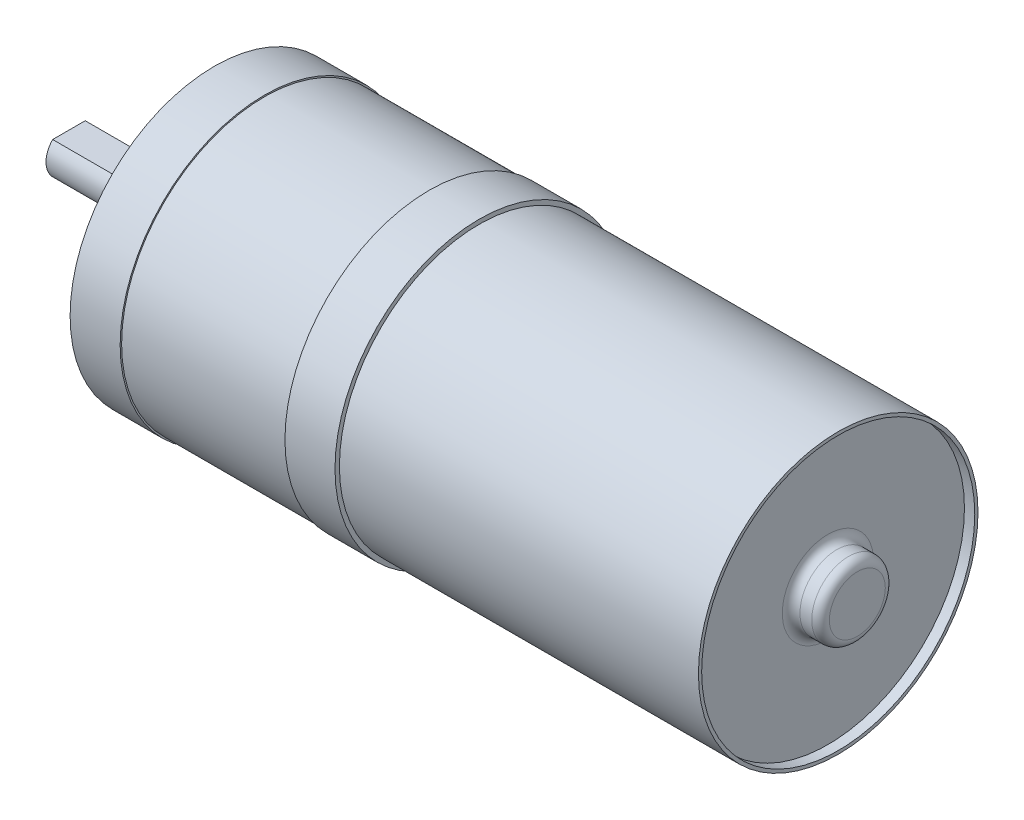
SolidWorks part; units mm, degrees
ref_plane "Front Plane" through (0, 0, 0) normal (0, 0, 1) x (1, 0, 0)
ref_plane "Top Plane" through (0, 0, 0) normal (0, 1, 0) x (1, 0, 0)
ref_plane "Right Plane" through (0, 0, 0) normal (1, 0, 0) x (0, 0, -1)
sketch "Sketch1" plane through (0, 0, 0) normal (1, 0, 0) x (0, 0, -1)
  circle A0 centre (0, 0) radius 12.065
extrude "Boss-Extrude1" add sketch "Sketch1" along normal blind 30.988
sketch "Sketch2" plane through (0, 0, 0) normal (-1, 0, 0) x (0, 0, 1)
  circle A0 centre (0, 0) radius 12.446
extrude "Boss-Extrude2" add sketch "Sketch2" along normal blind 4.318
sketch "Sketch3" plane through (-4.318, 0, 0) normal (-1, 0, 0) x (0, 0, 1)
  circle A0 centre (0, 0) radius 12.319
extrude "Boss-Extrude3" add sketch "Sketch3" along normal blind 14.224
sketch "Sketch4" plane through (-18.542, 0, 0) normal (-1, 0, 0) x (0, 0, 1)
  circle A0 centre (0, 0) radius 12.446
extrude "Boss-Extrude4" add sketch "Sketch4" along normal blind 4.318
sketch "Sketch5" plane through (-22.86, 0, 0) normal (-1, 0, 0) x (0, 0, 1)
  circle A0 centre (0, 0) radius 3.5052
extrude "Boss-Extrude5" add sketch "Sketch5" along normal blind 2.54
sketch "Sketch6" plane through (-25.4, 0, 0) normal (-1, 0, 0) x (0, 0, 1)
  circle A0 centre (0, 0) radius 1.9812
extrude "Boss-Extrude6" add sketch "Sketch6" along normal blind 10.0076
sketch "Sketch7" plane through (-35.4076, 0, 0) normal (-1, 0, 0) x (0, 0, 1)
  line L0 (-1.4048, 1.397) -> (1.4048, 1.397)
  arc A0 (1.4048, 1.397) -> (-1.4048, 1.397) centre (0, 0) ccw
  dimension "D1" = 1.397
extrude "Cut-Extrude1" cut sketch "Sketch7" against normal blind 7.9248
sketch "Sketch8" plane through (30.988, 0, 0) normal (1, 0, 0) x (0, 0, -1)
  circle A0 centre (0, 0) radius 11.7856
extrude "Cut-Extrude2" cut sketch "Sketch8" against normal blind 0.889
sketch "Sketch9" plane through (30.099, 0, 0) normal (1, 0, 0) x (0, 0, -1)
  circle A0 centre (0, 0) radius 3.175
extrude "Boss-Extrude7" add sketch "Sketch9" along normal blind 2.54
fillet "Fillet1" radius 0.762 2 edges at (30.099, 0, -3.175) (32.639, 0, -3.175)
sketch "Sketch10" plane through (-22.86, 0, 0) normal (-1, 0, 0) x (0, 0, 1)
  circle A0 centre (8.509, 0) radius 1.397
  circle A1 centre (-8.509, 0) radius 1.397
  dimension "D1" = 2.794
  dimension "D4" = 2.794
  dimension "D2" = 8.509
  dimension "D3" = 8.509
extrude "Cut-Extrude3" cut sketch "Sketch10" against normal blind 4.7498
